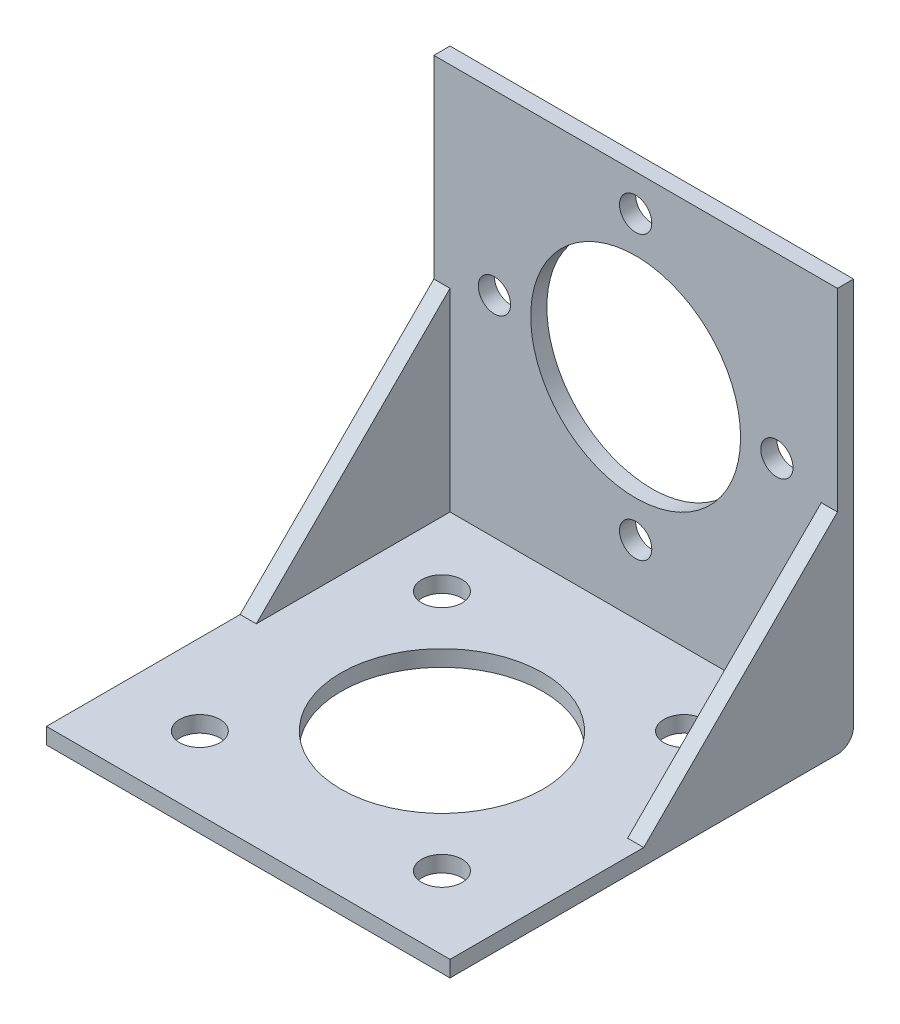
SolidWorks part; units mm, degrees
ref_plane "前视基准面" through (0, 0, 0) normal (0, 0, 1) x (1, 0, 0)
ref_plane "上视基准面" through (0, 0, 0) normal (0, 1, 0) x (1, 0, 0)
ref_plane "右视基准面" through (0, 0, 0) normal (1, 0, 0) x (0, 0, -1)
other "Configuration Table"
sketch "草图1" plane through (0, 0, 0) normal (1, 0, 0) x (0, 0, -1)
  line L0 (0, 0) -> (0, 50)
  line L1 (0, 0) -> (-50, 0)
  line L2 (-50, 0) -> (-50, 2)
  line L6 (-2, 50) -> (0, 50)
  line L7 (-50, 2) -> (-2, 2)
  line L8 (-2, 2) -> (-2, 50)
  dimension "D1" = 50
  dimension "D2" = 50
  dimension "D3" = 2
  dimension "D4" = 2
extrude "凸台-拉伸1" add sketch "草图1" along normal blind 50
sketch "草图2" plane through (50, 0, 0) normal (1, 0, 0) x (0, 0, -1)
  line L0 (-2, 26) -> (-26, 2)
  line L1 (-2, 50) -> (-2, 2) construction
  line L2 (-2, 2) -> (-50, 2) construction
  line L3 (-26, 2) -> (-2, 2)
  line L4 (-2, 2) -> (-2, 26)
extrude "凸台-拉伸2" add sketch "草图2" against normal blind 2
sketch "草图3" plane through (0, 0, 0) normal (-1, 0, 0) x (0, 0, 1)
  line L0 (2, 26) -> (26, 2)
  line L1 (26, 2) -> (2, 2)
  line L2 (2, 2) -> (2, 26)
extrude "凸台-拉伸4" add sketch "草图3" against normal blind 2
sketch "草图4" plane through (0, 0, 2) normal (0, 0, 1) x (1, 0, 0)
  line L0 (50, 0) -> (0, 0) construction
  line L1 (25, 28) -> (25, 50) construction
  line L2 (50, 50) -> (0, 50) construction
  line L3 (25, 28) -> (0, 28) construction
  line L4 (0, 50) -> (0, 26) construction
  circle A0 centre (25, 28) radius 13
  circle A1 centre (25, 28) radius 17.5 construction
  circle A2 centre (25, 45.5) radius 2
  circle A3 centre (42.5, 28) radius 2
  circle A4 centre (25, 10.5) radius 2
  circle A5 centre (7.5, 28) radius 2
  point P22 (25, 28)
  dimension "D2" = 26
  dimension "D3" = 35
  dimension "D4" = 4
  dimension "D1" = 28
extrude "切除-拉伸1" cut sketch "草图4" against normal through all
sketch "草图5" plane through (0, 2, 0) normal (0, 1, 0) x (1, 0, 0)
  line L0 (25, -2) -> (25, -50) construction
  line L1 (50, -2) -> (0, -2) construction
  line L2 (50, -50) -> (0, -50) construction
  line L3 (25, -26) -> (50, -26) construction
  line L6 (10, -41) -> (40, -41) construction
  line L7 (10, -41) -> (10, -11) construction
  line L8 (10, -11) -> (40, -11) construction
  line L9 (40, -41) -> (40, -11) construction
  line L10 (10, -41) -> (40, -11) construction
  line L11 (10, -11) -> (40, -41) construction
  circle A0 centre (25, -26) radius 12.5
  circle A1 centre (10, -11) radius 2.5
  circle A2 centre (40, -11) radius 2.5
  circle A3 centre (40, -41) radius 2.5
  circle A4 centre (10, -41) radius 2.5
  point P24 (25, -26)
  dimension "D1" = 25
  dimension "D4" = 5
  dimension "D2" = 30
  dimension "D3" = 30
  dimension "D5" = 4
extrude "切除-拉伸2" cut sketch "草图5" against normal through all
fillet "圆角2" radius 2 1 edges at (25, 0, 0)
